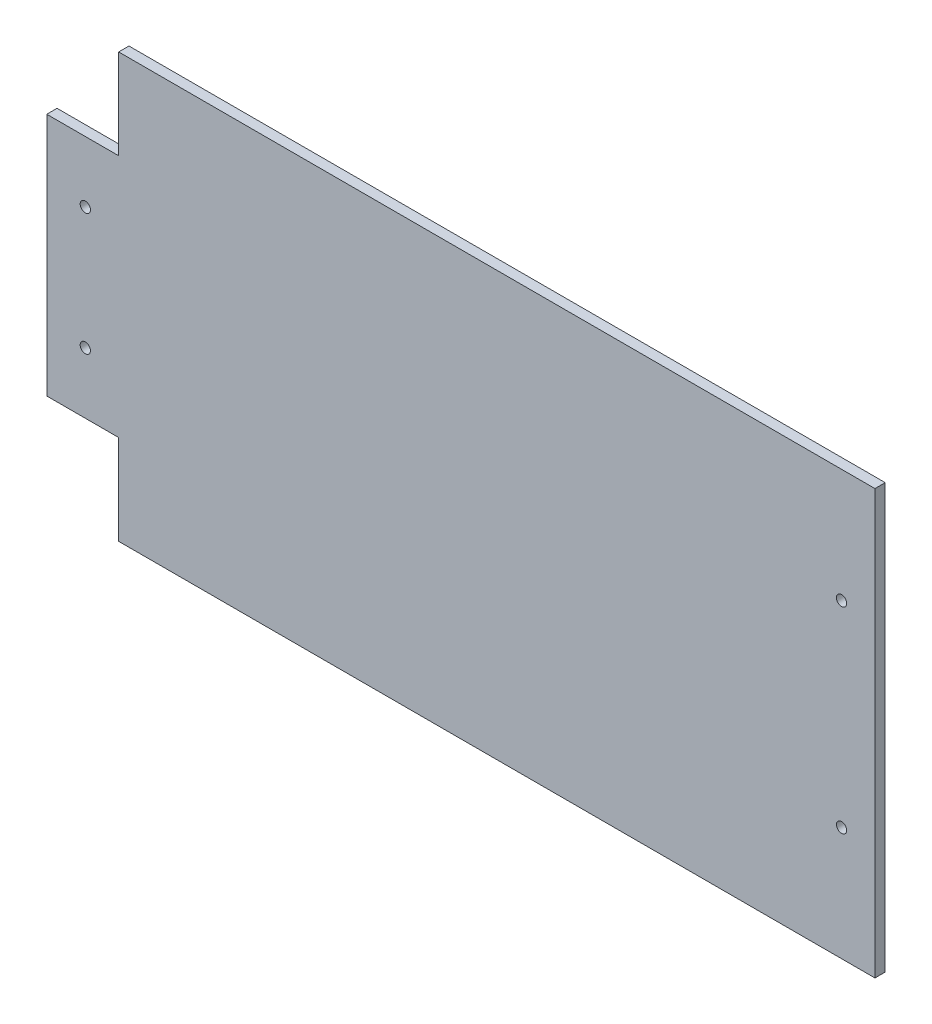
SolidWorks part; units mm, degrees
ref_plane "Front Plane" through (0, 0, 0) normal (0, 0, 1) x (1, 0, 0)
ref_plane "Top Plane" through (0, 0, 0) normal (0, 1, 0) x (1, 0, 0)
ref_plane "Right Plane" through (0, 0, 0) normal (1, 0, 0) x (0, 0, -1)
sketch "Sketch1" plane through (0, 0, 0) normal (0, 0, 1) x (1, 0, 0)
  line L8 (-196.1007, 58.6095) -> (-168.1007, 58.6095)
  line L9 (-168.1007, 58.6095) -> (-168.1007, 93.6095)
  line L10 (-168.1007, 93.6095) -> (126.2993, 93.6095)
  line L11 (126.2993, 93.6095) -> (126.2993, -71.3905)
  line L12 (126.2993, -71.3905) -> (-168.1007, -71.3905)
  line L13 (-168.1007, -71.3905) -> (-168.1007, -36.3905)
  line L14 (-168.1007, -36.3905) -> (-196.1007, -36.3905)
  line L15 (-196.1007, -36.3905) -> (-196.1007, 58.6095)
  circle A0 centre (-181.1007, 34.8595) radius 2
  circle A1 centre (-181.1007, -12.6405) radius 2
  circle A2 centre (113.2993, 49.3595) radius 2
  circle A3 centre (113.2993, -27.1405) radius 2
extrude "Boss-Extrude1" add sketch "Sketch1" along normal blind 4
